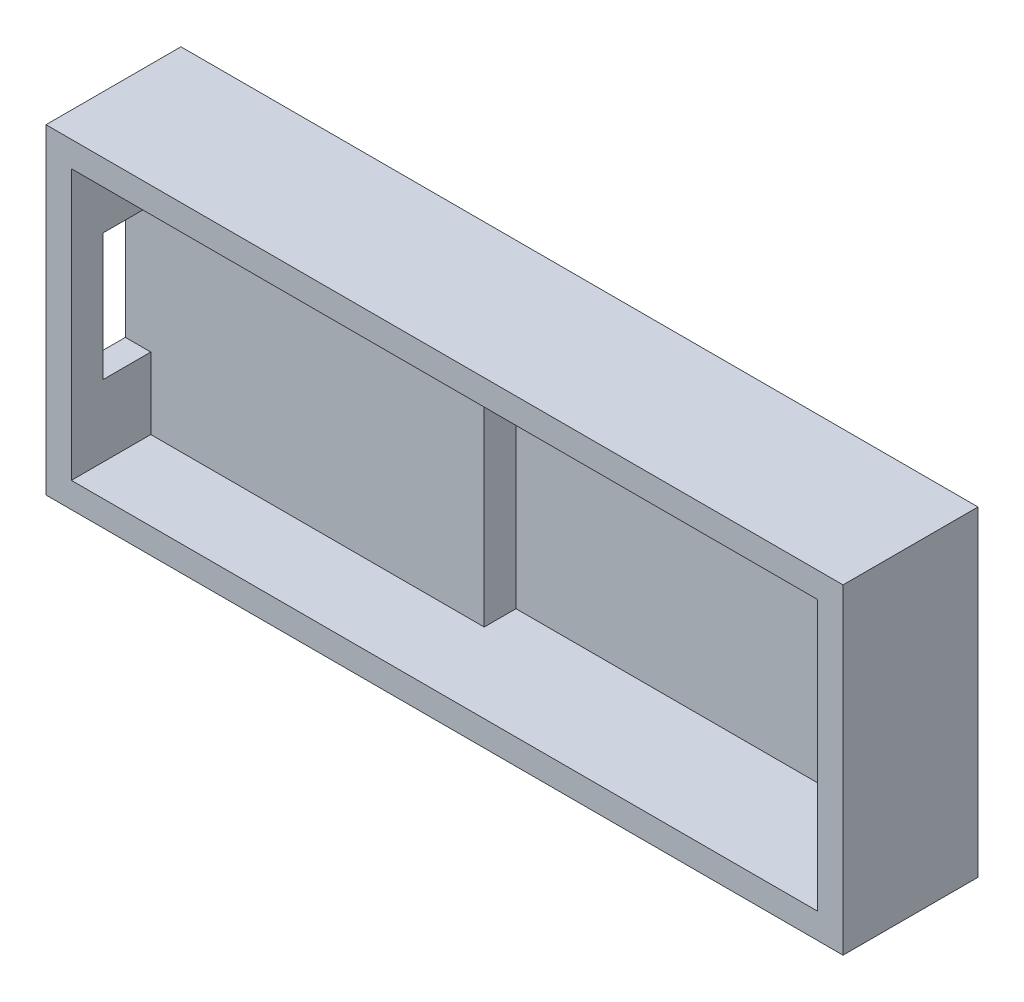
SolidWorks part; units mm, degrees
ref_plane "Front" through (0, 0, 0) normal (0, 0, 1) x (1, 0, 0)
ref_plane "Top" through (0, 0, 0) normal (0, 1, 0) x (1, 0, 0)
ref_plane "Right" through (0, 0, 0) normal (1, 0, 0) x (0, 0, -1)
sketch "Sketch1" plane through (0, 0, 0) normal (0, 0, 1) x (1, 0, 0)
  line L0 (-23.5, 8.5) -> (23.5, -8.5) construction
  line L1 (-23.5, 8.5) -> (23.5, 8.5)
  line L2 (-23.5, 8.5) -> (-23.5, -8.5)
  line L3 (-23.5, -8.5) -> (23.5, -8.5)
  line L4 (23.5, 8.5) -> (23.5, -8.5)
  dimension "D1" = 47
  dimension "D2" = 17
extrude "Boss-Extrude1" add sketch "Sketch1" along normal blind 1.5
sketch "Sketch3" plane through (0, 0, 1.5) normal (0, 0, 1) x (1, 0, 0)
  line L0 (-23.5, -8.5) -> (23.5, -8.5) construction
  line L1 (-23.5, 8.5) -> (-2.5, 8.5)
  line L2 (-23.5, 8.5) -> (-23.5, -8.5)
  line L3 (-23.5, -8.5) -> (-2.5, -8.5)
  line L4 (-2.5, 8.5) -> (-2.5, -8.5)
  line L6 (23.5, 8.5) -> (19.5, 8.5)
  line L7 (23.5, 8.5) -> (23.5, 6.5)
  line L8 (23.5, 6.5) -> (19.5, 6.5)
  line L9 (19.5, 8.5) -> (19.5, 6.5)
  line L10 (23.5, -8.5) -> (19.5, -8.5)
  line L11 (23.5, -8.5) -> (23.5, -6.5)
  line L12 (23.5, -6.5) -> (19.5, -6.5)
  line L13 (19.5, -8.5) -> (19.5, -6.5)
  dimension "D1" = 21
  dimension "D2" = 4
  dimension "D3" = 2
extrude "Boss-Extrude3" add sketch "Sketch3" along normal blind 2
sketch "Sketch2" plane through (0, 0, 0) normal (0, 0, 1) x (1, 0, 0)
  line L0 (-25.1, 10.1) -> (25.1, 10.1)
  line L1 (-23.5, 8.5) -> (23.5, 8.5)
  line L2 (-23.5, 8.5) -> (-23.5, -8.5)
  line L3 (-23.5, -8.5) -> (23.5, -8.5)
  line L4 (23.5, 8.5) -> (23.5, -8.5)
  line L5 (25.1, 10.1) -> (25.1, -10.1)
  line L6 (-25.1, -10.1) -> (25.1, -10.1)
  line L7 (-25.1, 10.1) -> (-25.1, -10.1)
  dimension "D1" = 1.6
extrude "Boss-Extrude2" add sketch "Sketch2" along normal offset from surface (8.5 mm away) 7 up to face at (15, -1.0625, 1.5) offset beyond the face yes
sketch "Sketch4" plane through (-23.5, 0, 0) normal (1, 0, 0) x (0, 0, -1)
  line L0 (-3.5, 4) -> (-3.5, -4)
  line L1 (-3.5, 4) -> (-6.5, 4)
  line L2 (-3.5, -4) -> (-6.5, -4)
  line L3 (-6.5, 4) -> (-6.5, -4)
  line L4 (-3.5, 8.5) -> (-3.5, -8.5) construction
  line L5 (0, 0) -> (-3.5, 0) construction
  dimension "D1" = 8
  dimension "D2" = 3
extrude "Cut-Extrude1" cut sketch "Sketch4" against normal through all
